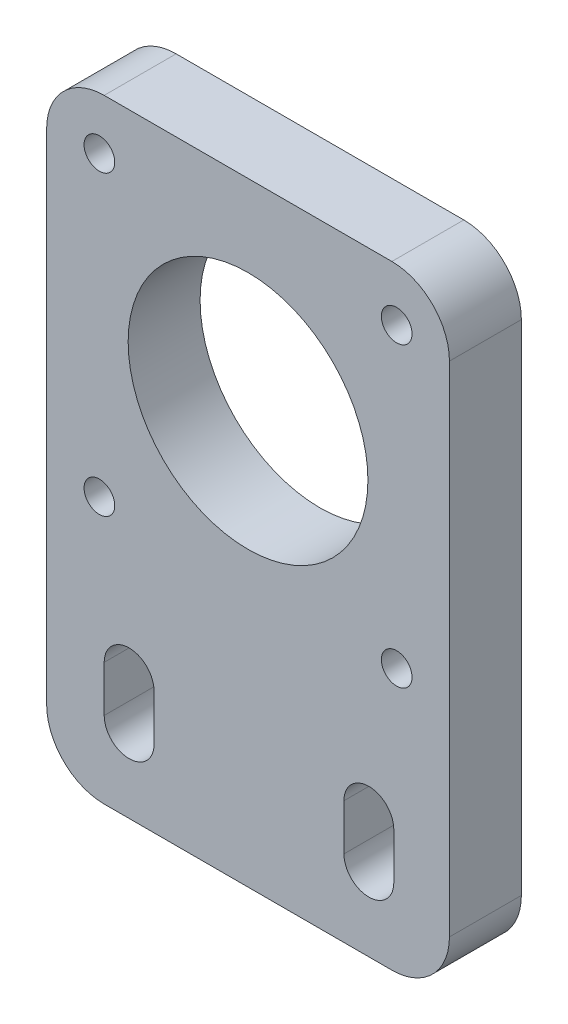
SolidWorks part; units mm, degrees
ref_plane "前视基准面" through (0, 0, 0) normal (0, 0, 1) x (1, 0, 0)
ref_plane "上视基准面" through (0, 0, 0) normal (0, 1, 0) x (1, 0, 0)
ref_plane "右视基准面" through (0, 0, 0) normal (1, 0, 0) x (0, 0, -1)
sketch "草图1" plane through (0, 0, 0) normal (0, 0, 1) x (1, 0, 0)
  line L1 (-11.5946, 38.5946) -> (18.4054, 38.5946)
  line L2 (-17.5946, 32.5946) -> (-17.5946, -19.4054)
  line L3 (-11.5946, -25.4054) -> (18.4054, -25.4054)
  line L4 (24.4054, 32.5946) -> (24.4054, -19.4054)
  line L18 (13.4054, -12.6054) -> (13.4054, -17.4054)
  line L19 (18.6054, -12.6054) -> (18.6054, -17.4054)
  line L20 (-11.5946, -12.6054) -> (-11.5946, -17.4054)
  line L21 (-6.3946, -12.6054) -> (-6.3946, -17.4054)
  circle A0 centre (3.4054, 17.5946) radius 12.5
  circle A1 centre (-12.0946, 33.0946) radius 1.6
  circle A2 centre (18.9054, 33.0946) radius 1.6
  circle A3 centre (18.9054, 2.0946) radius 1.6
  circle A4 centre (-12.0946, 2.0946) radius 1.6
  arc A9 (-11.5946, -17.4054) -> (-6.3946, -17.4054) centre (-8.9946, -17.4054) ccw
  arc A10 (18.6054, -12.6054) -> (13.4054, -12.6054) centre (16.0054, -12.6054) ccw
  arc A11 (-6.3946, -12.6054) -> (-11.5946, -12.6054) centre (-8.9946, -12.6054) ccw
  arc A12 (13.4054, -17.4054) -> (18.6054, -17.4054) centre (16.0054, -17.4054) ccw
  arc A13 (-17.5946, -19.4054) -> (-11.5946, -25.4054) centre (-11.5946, -19.4054) ccw
  arc A14 (18.4054, -25.4054) -> (24.4054, -19.4054) centre (18.4054, -19.4054) ccw
  arc A15 (24.4054, 32.5946) -> (18.4054, 38.5946) centre (18.4054, 32.5946) ccw
  arc A16 (-17.5946, 32.5946) -> (-11.5946, 38.5946) centre (-11.5946, 32.5946) cw
  point P10 (24.4054, -25.4054)
  point P13 (24.4054, 38.5946)
  point P16 (-17.5946, 38.5946)
  point P17 (0, 0)
  point P26 (0, 0)
  point P27 (0, 0)
  point P28 (0, 0)
  dimension "D4" = 25
  dimension "D8" = 3.2
  dimension "D9" = 3.2
  dimension "D10" = 3.2
  dimension "D11" = 3.2
  dimension "D3" = 6
  dimension "D1" = 42
  dimension "D2" = 64
extrude "凸台-拉伸1" add sketch "草图1" against normal blind 7.5
